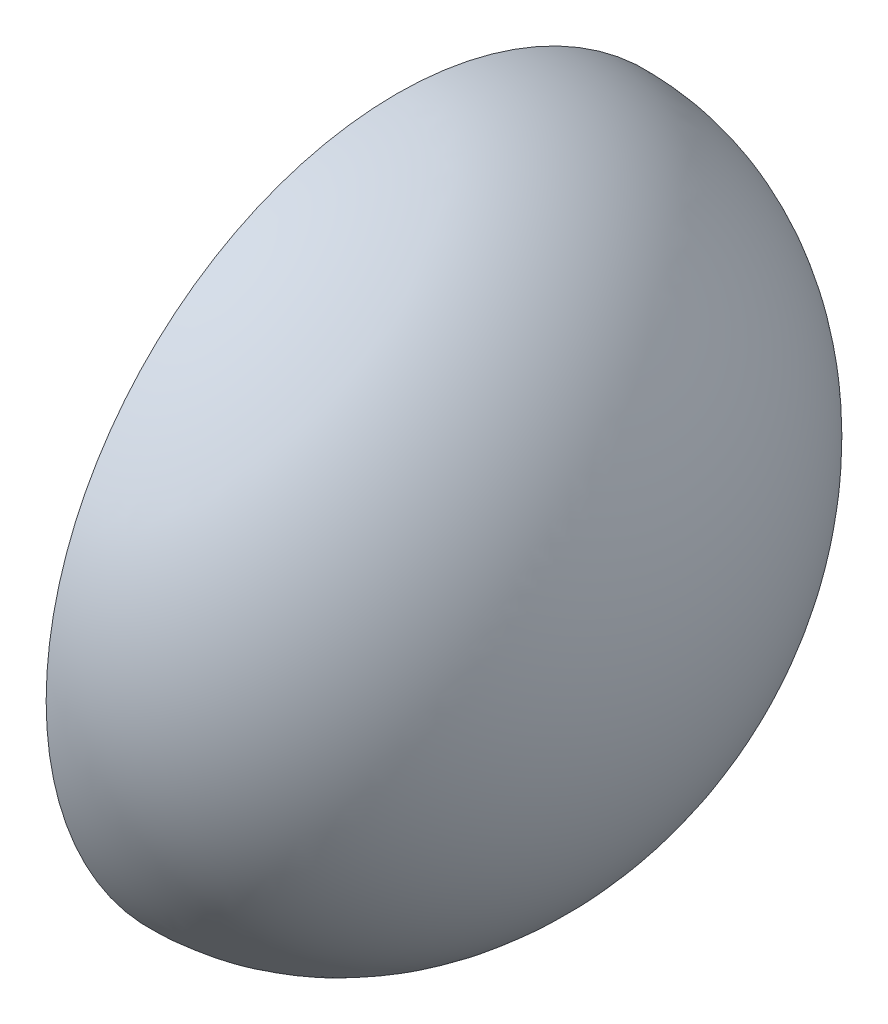
SolidWorks part; units mm, degrees
ref_plane "Front Plane" through (0, 0, 0) normal (0, 0, 1) x (1, 0, 0)
ref_plane "Top Plane" through (0, 0, 0) normal (0, 1, 0) x (1, 0, 0)
ref_plane "Right Plane" through (0, 0, 0) normal (1, 0, 0) x (0, 0, -1)
sketch "Sketch0" plane through (0, 0, 0) normal (0, 0, 1) x (1, 0, 0)
  line L3 (-14.7193, 0) -> (14.7193, 0) construction
  line L4 (-14.7193, 13.6144) -> (-14.7193, -13.6144) construction
  line L5 (3.4163, 10.6172) -> (-14.7193, 10.7696) construction
  line L6 (3.4163, 10.6172) -> (3.4163, -10.6172) construction
  line L7 (3.4163, -10.6172) -> (-14.7193, -10.7696) construction
  line L8 (-14.7193, 10.7696) -> (-14.7193, -10.7696) construction
  line L14 (3.4163, 7.8994) -> (3.4163, -7.8994) construction
  point P0 (3.4163, 0)
  dimension "H" = 11.303
  dimension "M" = 27.2288
  dimension "OD A" = 21.5392
  dimension "OD B" = 21.2344
  dimension "ID" = 15.7988
  dimension "L" = 29.4386
  dimension "C" = 18.1356
sketch "Sketch1" plane through (0, 0, 0) normal (0, 0, 1) x (1, 0, 0)
  line L0 (10.7221, 0) -> (11.7221, 0)
  line L1 (-14.7193, 0) -> (14.7193, 0) construction
  line L2 (-14.7193, 0) -> (14.7193, 0) construction
  line L3 (3.4163, -10.6172) -> (3.4163, -9.6172)
  ellipse E3 centre (3.4163, 0) end of major axis (3.4163, -10.6172) minor radius 8.3058 (3.4163, -10.6172) -> (11.7221, 0) ccw
  spline S0 degree 1 poles (3.4163, -9.6172) (10.7221, 0) knots 0 0 1 1 construction
  spline S1 degree 3 poles (3.4163, -9.6172) (4.3488, -9.6172) (6.1739, -9.1558) (8.6292, -7.0803) (10.3197, -3.871) (10.7221, -1.2666) (10.7221, 0) knots 0 0 0 0 0.392699 0.785398 1.178097 1.570796 1.570796 1.570796 1.570796
  dimension "D1" = 1
revolve "Revolve1" add sketch "Sketch1" angle 360 about L1
